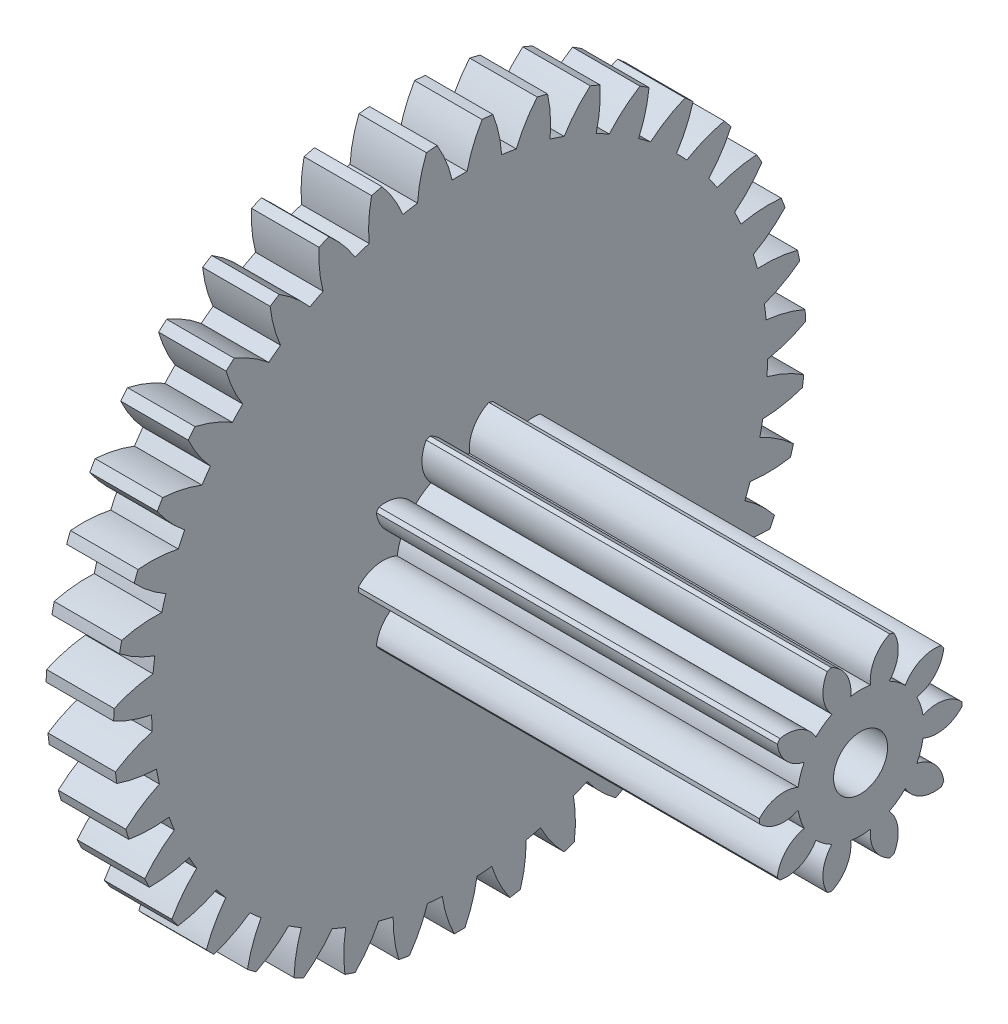
SolidWorks part; units mm, degrees
ref_plane "Plan de face" through (0, 0, 0) normal (0, 0, 1) x (1, 0, 0)
ref_plane "Plan de dessus" through (0, 0, 0) normal (0, 1, 0) x (1, 0, 0)
ref_plane "Plan de droite" through (0, 0, 0) normal (1, 0, 0) x (0, 0, -1)
ref_plane "Plan1" through (0, 0, 0) normal (0, 0, -1) x (-1, 0, 0)
sketch "Esquisse1" plane through (0, 0, 0) normal (0, 0, -1) x (-1, 0, 0)
  line L0 (-1, 5.125) -> (-1, 0)
  line L1 (-1, 0) -> (0, 0)
  line L2 (0, 0) -> (0, 5.125)
  line L3 (0, 5.125) -> (-1, 5.125)
  line L4 (-1, 0) -> (0, 0) construction
revolve "Révolution1" add sketch "Esquisse1" angle 360 about L4
sketch "Esquisse2" plane through (0, 0, 0) normal (-1, 0, 0) x (0, 0, 1)
  arc A0 (-0.4916, 5.1014) -> (-1.1491, 4.9945) centre (0, 0) ccw
  arc A1 (-1.1491, 4.9945) -> (-0.84, 4.4835) centre (-2.6433, 3.7415) cw
  arc A2 (-0.84, 4.4835) -> (-0.623, 4.5187) centre (0, 0) cw
  arc A3 (-0.623, 4.5187) -> (-0.4916, 5.1014) centre (1.3224, 4.386) cw
extrude "Enlèv. mat.-Extru.1" cut sketch "Esquisse2" against normal through all
sketch "Esquisse3" plane through (0, 0, 0) normal (-1, 0, 0) x (0, 0, 1)
  arc A0 (0.3331, 5.1142) -> (-0.3331, 5.1142) centre (0, 0) ccw
  arc A1 (-0.3331, 5.1142) -> (-0.1099, 4.5602) centre (-2.0089, 4.117) cw
  arc A2 (-0.1099, 4.5602) -> (0.1099, 4.5602) centre (0, 0) cw
  arc A3 (0.1099, 4.5602) -> (0.3331, 5.1142) centre (2.0089, 4.117) cw
extrude "Enlèv. mat.-Extru.2" cut sketch "Esquisse3" against normal through all
sketch "Esquisse4" plane through (0, 0, 0) normal (-1, 0, 0) x (0, 0, 1)
  arc A0 (1.1491, 4.9945) -> (0.4916, 5.1014) centre (0, 0) ccw
  arc A1 (0.4916, 5.1014) -> (0.623, 4.5187) centre (-1.3224, 4.386) cw
  arc A2 (0.623, 4.5187) -> (0.84, 4.4835) centre (0, 0) cw
  arc A3 (0.84, 4.4835) -> (1.1491, 4.9945) centre (2.6433, 3.7415) cw
extrude "Enlèv. mat.-Extru.3" cut sketch "Esquisse4" against normal through all
sketch "Esquisse5" plane through (0, 0, 0) normal (-1, 0, 0) x (0, 0, 1)
  arc A0 (1.9354, 4.7455) -> (1.3036, 4.9564) centre (0, 0) ccw
  arc A1 (1.3036, 4.9564) -> (1.3398, 4.3603) centre (-0.6017, 4.5413) cw
  arc A2 (1.3398, 4.3603) -> (1.5483, 4.2907) centre (0, 0) cw
  arc A3 (1.5483, 4.2907) -> (1.9354, 4.7455) centre (3.2092, 3.269) cw
extrude "Enlèv. mat.-Extru.4" cut sketch "Esquisse5" against normal through all
sketch "Esquisse6" plane through (0, 0, 0) normal (-1, 0, 0) x (0, 0, 1)
  arc A0 (2.6716, 4.3736) -> (2.0817, 4.6832) centre (0, 0) ccw
  arc A1 (2.0817, 4.6832) -> (2.0219, 4.0889) centre (0.1345, 4.579) cw
  arc A2 (2.0219, 4.0889) -> (2.2165, 3.9868) centre (0, 0) cw
  arc A3 (2.2165, 3.9868) -> (2.6716, 4.3736) centre (3.692, 2.7119) cw
extrude "Enlèv. mat.-Extru.5" cut sketch "Esquisse6" against normal through all
sketch "Esquisse7" plane through (0, 0, 0) normal (-1, 0, 0) x (0, 0, 1)
  arc A0 (3.3386, 3.8884) -> (2.806, 4.2886) centre (0, 0) ccw
  arc A1 (2.806, 4.2886) -> (2.6516, 3.7116) centre (0.8673, 4.4981) cw
  arc A2 (2.6516, 3.7116) -> (2.8273, 3.5796) centre (0, 0) cw
  arc A3 (2.8273, 3.5796) -> (3.3386, 3.8884) centre (4.0793, 2.0845) cw
extrude "Enlèv. mat.-Extru.6" cut sketch "Esquisse7" against normal through all
sketch "Esquisse8" plane through (0, 0, 0) normal (-1, 0, 0) x (0, 0, 1)
  arc A0 (3.9191, 3.3025) -> (3.4576, 3.7829) centre (0, 0) ccw
  arc A1 (3.4576, 3.7829) -> (3.2127, 3.2382) centre (1.5776, 4.3008) cw
  arc A2 (3.2127, 3.2382) -> (3.3649, 3.0797) centre (0, 0) cw
  arc A3 (3.3649, 3.0797) -> (3.9191, 3.3025) centre (4.3608, 1.4032) cw
extrude "Enlèv. mat.-Extru.7" cut sketch "Esquisse8" against normal through all
sketch "Esquisse9" plane through (0, 0, 0) normal (-1, 0, 0) x (0, 0, 1)
  arc A0 (4.3981, 2.6311) -> (4.0197, 3.1793) centre (0, 0) ccw
  arc A1 (4.0197, 3.1793) -> (3.6905, 2.6809) centre (2.2471, 3.992) cw
  arc A2 (3.6905, 2.6809) -> (3.8154, 2.5) centre (0, 0) cw
  arc A3 (3.8154, 2.5) -> (4.3981, 2.6311) centre (4.5294, 0.6855) cw
extrude "Enlèv. mat.-Extru.8" cut sketch "Esquisse9" against normal through all
sketch "Esquisse10" plane through (0, 0, 0) normal (-1, 0, 0) x (0, 0, 1)
  arc A0 (4.7632, 1.8915) -> (4.4776, 2.4933) centre (0, 0) ccw
  arc A1 (4.4776, 2.4933) -> (4.0728, 2.0542) centre (2.8584, 3.5799) cw
  arc A2 (4.0728, 2.0542) -> (4.167, 1.8556) centre (0, 0) cw
  arc A3 (4.167, 1.8556) -> (4.7632, 1.8915) centre (4.5807, -0.05) cw
extrude "Enlèv. mat.-Extru.9" cut sketch "Esquisse10" against normal through all
sketch "Esquisse11" plane through (0, 0, 0) normal (-1, 0, 0) x (0, 0, 1)
  arc A0 (5.0049, 1.1029) -> (4.8196, 1.7428) centre (0, 0) ccw
  arc A1 (4.8196, 1.7428) -> (4.3496, 1.3743) centre (3.3956, 3.075) cw
  arc A2 (4.3496, 1.3743) -> (4.4107, 1.1632) centre (0, 0) cw
  arc A3 (4.4107, 1.1632) -> (5.0049, 1.1029) centre (4.5134, -0.7841) cw
extrude "Enlèv. mat.-Extru.10" cut sketch "Esquisse11" against normal through all
sketch "Esquisse12" plane through (0, 0, 0) normal (-1, 0, 0) x (0, 0, 1)
  arc A0 (5.117, 0.2858) -> (5.0367, 0.9471) centre (0, 0) ccw
  arc A1 (5.0367, 0.9471) -> (4.5137, 0.6588) centre (3.8449, 2.4905) cw
  arc A2 (4.5137, 0.6588) -> (4.5402, 0.4406) centre (0, 0) cw
  arc A3 (4.5402, 0.4406) -> (5.117, 0.2858) centre (4.3292, -1.498) cw
extrude "Enlèv. mat.-Extru.11" cut sketch "Esquisse12" against normal through all
sketch "Esquisse13" plane through (0, 0, 0) normal (-1, 0, 0) x (0, 0, 1)
  arc A0 (5.0966, -0.5387) -> (5.1234, 0.1269) centre (0, 0) ccw
  arc A1 (5.1234, 0.1269) -> (4.5609, -0.0738) centre (4.1946, 1.8415) cw
  arc A2 (4.5609, -0.0738) -> (4.5521, -0.2934) centre (0, 0) cw
  arc A3 (4.5521, -0.2934) -> (5.0966, -0.5387) centre (4.0328, -2.173) cw
extrude "Enlèv. mat.-Extru.12" cut sketch "Esquisse13" against normal through all
sketch "Esquisse14" plane through (0, 0, 0) normal (-1, 0, 0) x (0, 0, 1)
  arc A0 (4.9442, -1.3493) -> (5.0774, -0.6966) centre (0, 0) ccw
  arc A1 (5.0774, -0.6966) -> (4.49, -0.8045) centre (4.4357, 1.1448) cw
  arc A2 (4.49, -0.8045) -> (4.446, -1.0198) centre (0, 0) cw
  arc A3 (4.446, -1.0198) -> (4.9442, -1.3493) centre (3.632, -2.7918) cw
extrude "Enlèv. mat.-Extru.13" cut sketch "Esquisse14" against normal through all
sketch "Esquisse15" plane through (0, 0, 0) normal (-1, 0, 0) x (0, 0, 1)
  arc A0 (4.6637, -2.1249) -> (4.8999, -1.5021) centre (0, 0) ccw
  arc A1 (4.8999, -1.5021) -> (4.3028, -1.5143) centre (4.5619, 0.4184) cw
  arc A2 (4.3028, -1.5143) -> (4.2249, -1.7198) centre (0, 0) cw
  arc A3 (4.2249, -1.7198) -> (4.6637, -2.1249) centre (3.1371, -3.3382) cw
extrude "Enlèv. mat.-Extru.14" cut sketch "Esquisse15" against normal through all
sketch "Esquisse16" plane through (0, 0, 0) normal (-1, 0, 0) x (0, 0, 1)
  arc A0 (4.2625, -2.8455) -> (4.5955, -2.2686) centre (0, 0) ccw
  arc A1 (4.5955, -2.2686) -> (4.0042, -2.1849) centre (4.5699, -0.3188) cw
  arc A2 (4.0042, -2.1849) -> (3.8943, -2.3753) centre (0, 0) cw
  arc A3 (3.8943, -2.3753) -> (4.2625, -2.8455) centre (2.561, -3.7982) cw
extrude "Enlèv. mat.-Extru.15" cut sketch "Esquisse16" against normal through all
sketch "Esquisse17" plane through (0, 0, 0) normal (-1, 0, 0) x (0, 0, 1)
  arc A0 (3.7508, -3.4924) -> (4.1721, -2.9764) centre (0, 0) ccw
  arc A1 (4.1721, -2.9764) -> (3.6018, -2.7989) centre (4.4596, -1.0477) cw
  arc A2 (3.6018, -2.7989) -> (3.4628, -2.9692) centre (0, 0) cw
  arc A3 (3.4628, -2.9692) -> (3.7508, -3.4924) centre (1.9186, -4.1599) cw
extrude "Enlèv. mat.-Extru.16" cut sketch "Esquisse17" against normal through all
sketch "Esquisse18" plane through (0, 0, 0) normal (-1, 0, 0) x (0, 0, 1)
  arc A0 (3.142, -4.0489) -> (3.6406, -3.6071) centre (0, 0) ccw
  arc A1 (3.6406, -3.6071) -> (3.1062, -3.3405) centre (4.2338, -1.7495) cw
  arc A2 (3.1062, -3.3405) -> (2.9417, -3.4862) centre (0, 0) cw
  arc A3 (2.9417, -3.4862) -> (3.142, -4.0489) centre (1.2264, -4.4138) cw
extrude "Enlèv. mat.-Extru.17" cut sketch "Esquisse18" against normal through all
sketch "Esquisse19" plane through (0, 0, 0) normal (-1, 0, 0) x (0, 0, 1)
  arc A0 (2.4518, -4.5005) -> (3.0149, -4.1444) centre (0, 0) ccw
  arc A1 (3.0149, -4.1444) -> (2.5301, -3.7955) centre (3.8983, -2.406) cw
  arc A2 (2.5301, -3.7955) -> (2.3444, -3.9129) centre (0, 0) cw
  arc A3 (2.3444, -3.9129) -> (2.4518, -4.5005) centre (0.5025, -4.5534) cw
extrude "Enlèv. mat.-Extru.18" cut sketch "Esquisse19" against normal through all
sketch "Esquisse20" plane through (0, 0, 0) normal (-1, 0, 0) x (0, 0, 1)
  arc A0 (1.6982, -4.8355) -> (2.311, -4.5744) centre (0, 0) ccw
  arc A1 (2.311, -4.5744) -> (1.8885, -4.1522) centre (3.4619, -3.0002) cw
  arc A2 (1.8885, -4.1522) -> (1.6863, -4.2383) centre (0, 0) cw
  arc A3 (1.6863, -4.2383) -> (1.6982, -4.8355) centre (-0.2344, -4.575) cw
extrude "Enlèv. mat.-Extru.19" cut sketch "Esquisse20" against normal through all
sketch "Esquisse21" plane through (0, 0, 0) normal (-1, 0, 0) x (0, 0, 1)
  arc A0 (0.9005, -5.0453) -> (1.5473, -4.8858) centre (0, 0) ccw
  arc A1 (1.5473, -4.8858) -> (1.198, -4.4014) centre (2.9358, -3.5167) cw
  arc A2 (1.198, -4.4014) -> (0.9846, -4.454) centre (0, 0) cw
  arc A3 (0.9846, -4.454) -> (0.9005, -5.0453) centre (-0.9652, -4.4782) cw
extrude "Enlèv. mat.-Extru.20" cut sketch "Esquisse21" against normal through all
sketch "Esquisse22" plane through (0, 0, 0) normal (-1, 0, 0) x (0, 0, 1)
  arc A0 (0.0795, -5.1244) -> (0.7435, -5.0708) centre (0, 0) ccw
  arc A1 (0.7435, -5.0708) -> (0.4765, -4.5365) centre (2.3336, -3.942) cw
  arc A2 (0.4765, -4.5365) -> (0.2574, -4.5542) centre (0, 0) cw
  arc A3 (0.2574, -4.5542) -> (0.0795, -5.1244) centre (-1.6711, -4.2653) cw
extrude "Enlèv. mat.-Extru.21" cut sketch "Esquisse22" against normal through all
sketch "Esquisse23" plane through (0, 0, 0) normal (-1, 0, 0) x (0, 0, 1)
  arc A0 (-0.7435, -5.0708) -> (-0.0795, -5.1244) centre (0, 0) ccw
  arc A1 (-0.0795, -5.1244) -> (-0.2574, -4.5542) centre (1.6711, -4.2653) cw
  arc A2 (-0.2574, -4.5542) -> (-0.4765, -4.5365) centre (0, 0) cw
  arc A3 (-0.4765, -4.5365) -> (-0.7435, -5.0708) centre (-2.3336, -3.942) cw
extrude "Enlèv. mat.-Extru.22" cut sketch "Esquisse23" against normal through all
sketch "Esquisse24" plane through (0, 0, 0) normal (-1, 0, 0) x (0, 0, 1)
  arc A0 (-1.5473, -4.8858) -> (-0.9005, -5.0453) centre (0, 0) ccw
  arc A1 (-0.9005, -5.0453) -> (-0.9846, -4.454) centre (0.9652, -4.4782) cw
  arc A2 (-0.9846, -4.454) -> (-1.198, -4.4014) centre (0, 0) cw
  arc A3 (-1.198, -4.4014) -> (-1.5473, -4.8858) centre (-2.9358, -3.5167) cw
extrude "Enlèv. mat.-Extru.23" cut sketch "Esquisse24" against normal through all
sketch "Esquisse25" plane through (0, 0, 0) normal (-1, 0, 0) x (0, 0, 1)
  arc A0 (-2.311, -4.5744) -> (-1.6982, -4.8355) centre (0, 0) ccw
  arc A1 (-1.6982, -4.8355) -> (-1.6863, -4.2383) centre (0.2344, -4.575) cw
  arc A2 (-1.6863, -4.2383) -> (-1.8885, -4.1522) centre (0, 0) cw
  arc A3 (-1.8885, -4.1522) -> (-2.311, -4.5744) centre (-3.4619, -3.0002) cw
extrude "Enlèv. mat.-Extru.24" cut sketch "Esquisse25" against normal through all
sketch "Esquisse26" plane through (0, 0, 0) normal (-1, 0, 0) x (0, 0, 1)
  arc A0 (-3.0149, -4.1444) -> (-2.4518, -4.5005) centre (0, 0) ccw
  arc A1 (-2.4518, -4.5005) -> (-2.3444, -3.9129) centre (-0.5025, -4.5534) cw
  arc A2 (-2.3444, -3.9129) -> (-2.5301, -3.7955) centre (0, 0) cw
  arc A3 (-2.5301, -3.7955) -> (-3.0149, -4.1444) centre (-3.8983, -2.406) cw
extrude "Enlèv. mat.-Extru.25" cut sketch "Esquisse26" against normal through all
sketch "Esquisse27" plane through (0, 0, 0) normal (-1, 0, 0) x (0, 0, 1)
  arc A0 (-3.6406, -3.6071) -> (-3.142, -4.0489) centre (0, 0) ccw
  arc A1 (-3.142, -4.0489) -> (-2.9417, -3.4862) centre (-1.2264, -4.4138) cw
  arc A2 (-2.9417, -3.4862) -> (-3.1062, -3.3405) centre (0, 0) cw
  arc A3 (-3.1062, -3.3405) -> (-3.6406, -3.6071) centre (-4.2338, -1.7495) cw
extrude "Enlèv. mat.-Extru.26" cut sketch "Esquisse27" against normal through all
sketch "Esquisse28" plane through (0, 0, 0) normal (-1, 0, 0) x (0, 0, 1)
  arc A0 (-4.1721, -2.9764) -> (-3.7508, -3.4924) centre (0, 0) ccw
  arc A1 (-3.7508, -3.4924) -> (-3.4628, -2.9692) centre (-1.9186, -4.1599) cw
  arc A2 (-3.4628, -2.9692) -> (-3.6018, -2.7989) centre (0, 0) cw
  arc A3 (-3.6018, -2.7989) -> (-4.1721, -2.9764) centre (-4.4596, -1.0477) cw
extrude "Enlèv. mat.-Extru.27" cut sketch "Esquisse28" against normal through all
sketch "Esquisse29" plane through (0, 0, 0) normal (-1, 0, 0) x (0, 0, 1)
  arc A0 (-4.5955, -2.2686) -> (-4.2625, -2.8455) centre (0, 0) ccw
  arc A1 (-4.2625, -2.8455) -> (-3.8943, -2.3753) centre (-2.561, -3.7982) cw
  arc A2 (-3.8943, -2.3753) -> (-4.0042, -2.1849) centre (0, 0) cw
  arc A3 (-4.0042, -2.1849) -> (-4.5955, -2.2686) centre (-4.5699, -0.3188) cw
extrude "Enlèv. mat.-Extru.28" cut sketch "Esquisse29" against normal through all
sketch "Esquisse30" plane through (0, 0, 0) normal (-1, 0, 0) x (0, 0, 1)
  arc A0 (-4.8999, -1.5021) -> (-4.6637, -2.1249) centre (0, 0) ccw
  arc A1 (-4.6637, -2.1249) -> (-4.2249, -1.7198) centre (-3.1371, -3.3382) cw
  arc A2 (-4.2249, -1.7198) -> (-4.3028, -1.5143) centre (0, 0) cw
  arc A3 (-4.3028, -1.5143) -> (-4.8999, -1.5021) centre (-4.5619, 0.4184) cw
extrude "Enlèv. mat.-Extru.29" cut sketch "Esquisse30" against normal through all
sketch "Esquisse31" plane through (0, 0, 0) normal (-1, 0, 0) x (0, 0, 1)
  arc A0 (-5.0774, -0.6966) -> (-4.9442, -1.3493) centre (0, 0) ccw
  arc A1 (-4.9442, -1.3493) -> (-4.446, -1.0198) centre (-3.632, -2.7918) cw
  arc A2 (-4.446, -1.0198) -> (-4.49, -0.8045) centre (0, 0) cw
  arc A3 (-4.49, -0.8045) -> (-5.0774, -0.6966) centre (-4.4357, 1.1448) cw
extrude "Enlèv. mat.-Extru.30" cut sketch "Esquisse31" against normal through all
sketch "Esquisse32" plane through (0, 0, 0) normal (-1, 0, 0) x (0, 0, 1)
  arc A0 (-5.1234, 0.1269) -> (-5.0966, -0.5387) centre (0, 0) ccw
  arc A1 (-5.0966, -0.5387) -> (-4.5521, -0.2934) centre (-4.0328, -2.173) cw
  arc A2 (-4.5521, -0.2934) -> (-4.5609, -0.0738) centre (0, 0) cw
  arc A3 (-4.5609, -0.0738) -> (-5.1234, 0.1269) centre (-4.1946, 1.8415) cw
extrude "Enlèv. mat.-Extru.31" cut sketch "Esquisse32" against normal through all
sketch "Esquisse33" plane through (0, 0, 0) normal (-1, 0, 0) x (0, 0, 1)
  arc A0 (-5.0367, 0.9471) -> (-5.117, 0.2858) centre (0, 0) ccw
  arc A1 (-5.117, 0.2858) -> (-4.5402, 0.4406) centre (-4.3292, -1.498) cw
  arc A2 (-4.5402, 0.4406) -> (-4.5137, 0.6588) centre (0, 0) cw
  arc A3 (-4.5137, 0.6588) -> (-5.0367, 0.9471) centre (-3.8449, 2.4905) cw
extrude "Enlèv. mat.-Extru.32" cut sketch "Esquisse33" against normal through all
sketch "Esquisse34" plane through (0, 0, 0) normal (-1, 0, 0) x (0, 0, 1)
  arc A0 (-4.8196, 1.7428) -> (-5.0049, 1.1029) centre (0, 0) ccw
  arc A1 (-5.0049, 1.1029) -> (-4.4107, 1.1632) centre (-4.5134, -0.7841) cw
  arc A2 (-4.4107, 1.1632) -> (-4.3496, 1.3743) centre (0, 0) cw
  arc A3 (-4.3496, 1.3743) -> (-4.8196, 1.7428) centre (-3.3956, 3.075) cw
extrude "Enlèv. mat.-Extru.33" cut sketch "Esquisse34" against normal through all
sketch "Esquisse35" plane through (0, 0, 0) normal (-1, 0, 0) x (0, 0, 1)
  arc A0 (-4.4776, 2.4933) -> (-4.7632, 1.8915) centre (0, 0) ccw
  arc A1 (-4.7632, 1.8915) -> (-4.167, 1.8556) centre (-4.5807, -0.05) cw
  arc A2 (-4.167, 1.8556) -> (-4.0728, 2.0542) centre (0, 0) cw
  arc A3 (-4.0728, 2.0542) -> (-4.4776, 2.4933) centre (-2.8584, 3.5799) cw
extrude "Enlèv. mat.-Extru.34" cut sketch "Esquisse35" against normal through all
sketch "Esquisse36" plane through (0, 0, 0) normal (-1, 0, 0) x (0, 0, 1)
  arc A0 (-4.0197, 3.1793) -> (-4.3981, 2.6311) centre (0, 0) ccw
  arc A1 (-4.3981, 2.6311) -> (-3.8154, 2.5) centre (-4.5294, 0.6855) cw
  arc A2 (-3.8154, 2.5) -> (-3.6905, 2.6809) centre (0, 0) cw
  arc A3 (-3.6905, 2.6809) -> (-4.0197, 3.1793) centre (-2.2471, 3.992) cw
extrude "Enlèv. mat.-Extru.35" cut sketch "Esquisse36" against normal through all
sketch "Esquisse37" plane through (0, 0, 0) normal (-1, 0, 0) x (0, 0, 1)
  arc A0 (-3.4576, 3.7829) -> (-3.9191, 3.3025) centre (0, 0) ccw
  arc A1 (-3.9191, 3.3025) -> (-3.3649, 3.0797) centre (-4.3608, 1.4032) cw
  arc A2 (-3.3649, 3.0797) -> (-3.2127, 3.2382) centre (0, 0) cw
  arc A3 (-3.2127, 3.2382) -> (-3.4576, 3.7829) centre (-1.5776, 4.3008) cw
extrude "Enlèv. mat.-Extru.36" cut sketch "Esquisse37" against normal through all
sketch "Esquisse38" plane through (0, 0, 0) normal (-1, 0, 0) x (0, 0, 1)
  arc A0 (-2.806, 4.2886) -> (-3.3386, 3.8884) centre (0, 0) ccw
  arc A1 (-3.3386, 3.8884) -> (-2.8273, 3.5796) centre (-4.0793, 2.0845) cw
  arc A2 (-2.8273, 3.5796) -> (-2.6516, 3.7116) centre (0, 0) cw
  arc A3 (-2.6516, 3.7116) -> (-2.806, 4.2886) centre (-0.8673, 4.4981) cw
extrude "Enlèv. mat.-Extru.37" cut sketch "Esquisse38" against normal through all
sketch "Esquisse39" plane through (0, 0, 0) normal (-1, 0, 0) x (0, 0, 1)
  arc A0 (-2.0817, 4.6832) -> (-2.6716, 4.3736) centre (0, 0) ccw
  arc A1 (-2.6716, 4.3736) -> (-2.2165, 3.9868) centre (-3.692, 2.7119) cw
  arc A2 (-2.2165, 3.9868) -> (-2.0219, 4.0889) centre (0, 0) cw
  arc A3 (-2.0219, 4.0889) -> (-2.0817, 4.6832) centre (-0.1345, 4.579) cw
extrude "Enlèv. mat.-Extru.38" cut sketch "Esquisse39" against normal through all
sketch "Esquisse40" plane through (0, 0, 0) normal (-1, 0, 0) x (0, 0, 1)
  arc A0 (-1.3036, 4.9564) -> (-1.9354, 4.7455) centre (0, 0) ccw
  arc A1 (-1.9354, 4.7455) -> (-1.5483, 4.2907) centre (-3.2092, 3.269) cw
  arc A2 (-1.5483, 4.2907) -> (-1.3398, 4.3603) centre (0, 0) cw
  arc A3 (-1.3398, 4.3603) -> (-1.3036, 4.9564) centre (0.6017, 4.5413) cw
extrude "Enlèv. mat.-Extru.39" cut sketch "Esquisse40" against normal through all
sketch "Esquisse41" plane through (1, 0, 0) normal (1, 0, 0) x (0, 0, -1)
  arc A0 (0.6621, 0.6623) -> (1.1939, 0.9081) centre (1.098, 0.4174) cw
  arc A1 (1.1939, 0.9081) -> (1.2326, 0.8548) centre (0, 0) cw
  arc A2 (1.2326, 0.8548) -> (0.8345, 0.425) centre (0.7362, 0.9152) cw
  arc A3 (0.8345, 0.425) -> (0.9249, 0.1467) centre (0, 0) cw
  arc A4 (0.9249, 0.1467) -> (1.4996, 0.0329) centre (1.1336, -0.3077) cw
  arc A5 (1.4996, 0.0329) -> (1.4996, -0.0329) centre (0, 0) cw
  arc A6 (1.4996, -0.0329) -> (0.9249, -0.1467) centre (1.1336, 0.3077) cw
  arc A7 (0.9249, -0.1467) -> (0.8345, -0.425) centre (0, 0) cw
  arc A8 (0.8345, -0.425) -> (1.2326, -0.8548) centre (0.7362, -0.9152) cw
  arc A9 (1.2326, -0.8548) -> (1.1939, -0.9081) centre (0, 0) cw
  arc A10 (1.1939, -0.9081) -> (0.6621, -0.6623) centre (1.098, -0.4174) cw
  arc A11 (0.6621, -0.6623) -> (0.4253, -0.8343) centre (0, 0) cw
  arc A12 (0.4253, -0.8343) -> (0.4947, -1.4161) centre (0.0577, -1.1732) cw
  arc A13 (0.4947, -1.4161) -> (0.4321, -1.4364) centre (0, 0) cw
  arc A14 (0.4321, -1.4364) -> (0.1463, -0.925) centre (0.6429, -0.983) cw
  arc A15 (0.1463, -0.925) -> (-0.1463, -0.925) centre (0, 0) cw
  arc A16 (-0.1463, -0.925) -> (-0.4321, -1.4364) centre (-0.6429, -0.983) cw
  arc A17 (-0.4321, -1.4364) -> (-0.4947, -1.4161) centre (0, 0) cw
  arc A18 (-0.4947, -1.4161) -> (-0.4253, -0.8343) centre (-0.0577, -1.1732) cw
  arc A19 (-0.4253, -0.8343) -> (-0.6621, -0.6623) centre (0, 0) cw
  arc A20 (-0.6621, -0.6623) -> (-1.1939, -0.9081) centre (-1.098, -0.4174) cw
  arc A21 (-1.1939, -0.9081) -> (-1.2326, -0.8548) centre (0, 0) cw
  arc A22 (-1.2326, -0.8548) -> (-0.8345, -0.425) centre (-0.7362, -0.9152) cw
  arc A23 (-0.8345, -0.425) -> (-0.9249, -0.1467) centre (0, 0) cw
  arc A24 (-0.9249, -0.1467) -> (-1.4996, -0.0329) centre (-1.1336, 0.3077) cw
  arc A25 (-1.4996, -0.0329) -> (-1.4996, 0.0329) centre (0, 0) cw
  arc A26 (-1.4996, 0.0329) -> (-0.9249, 0.1467) centre (-1.1336, -0.3077) cw
  arc A27 (-0.9249, 0.1467) -> (-0.8345, 0.425) centre (0, 0) cw
  arc A28 (-0.8345, 0.425) -> (-1.2326, 0.8548) centre (-0.7362, 0.9152) cw
  arc A29 (-1.2326, 0.8548) -> (-1.1939, 0.9081) centre (0, 0) cw
  arc A30 (-1.1939, 0.9081) -> (-0.6621, 0.6623) centre (-1.098, 0.4174) cw
  arc A31 (-0.6621, 0.6623) -> (-0.4253, 0.8343) centre (0, 0) cw
  arc A32 (-0.4253, 0.8343) -> (-0.4947, 1.4161) centre (-0.0577, 1.1732) cw
  arc A33 (-0.4947, 1.4161) -> (-0.4321, 1.4364) centre (0, 0) cw
  arc A34 (-0.4321, 1.4364) -> (-0.1463, 0.925) centre (-0.6429, 0.983) cw
  arc A35 (-0.1463, 0.925) -> (0.1463, 0.925) centre (0, 0) cw
  arc A36 (0.1463, 0.925) -> (0.4321, 1.4364) centre (0.6429, 0.983) cw
  arc A37 (0.4321, 1.4364) -> (0.4947, 1.4161) centre (0, 0) cw
  arc A38 (0.4947, 1.4161) -> (0.4253, 0.8343) centre (0.0577, 1.1732) cw
  arc A39 (0.4253, 0.8343) -> (0.6621, 0.6623) centre (0, 0) cw
extrude "Boss.-Extru.1" add sketch "Esquisse41" along normal blind 5.9385
hole_wizard "Diamètre du perçage Ø0.8 (0.8)1" positions "Esquisse43" profile "Esquisse42" hole size "Ø0.8" standard "Ansi Metric"
sketch "Esquisse43" plane through (0, 0, 0) normal (-1, 0, 0) x (0, 0, 1)
  point P0 (0, 0)
sketch "Esquisse42" plane through (0, 0, 0) normal (0, 1, 0) x (0, 0, 1)
  line L0 (0, 0) -> (0, 6.9385)
  line L1 (0, 6.9385) -> (0.4, 6.9385)
  line L2 (0.4, 6.9385) -> (0.4, 0)
  line L5 (0.4, 0) -> (0, 0)
  line L11 (0, -6.35) -> (0, 107.95) construction
  dimension "Diamètre du perçage jusqu'au prochain" = 0.8
  dimension "Profondeur du perçage jusqu'au prochain" = 6.9385
